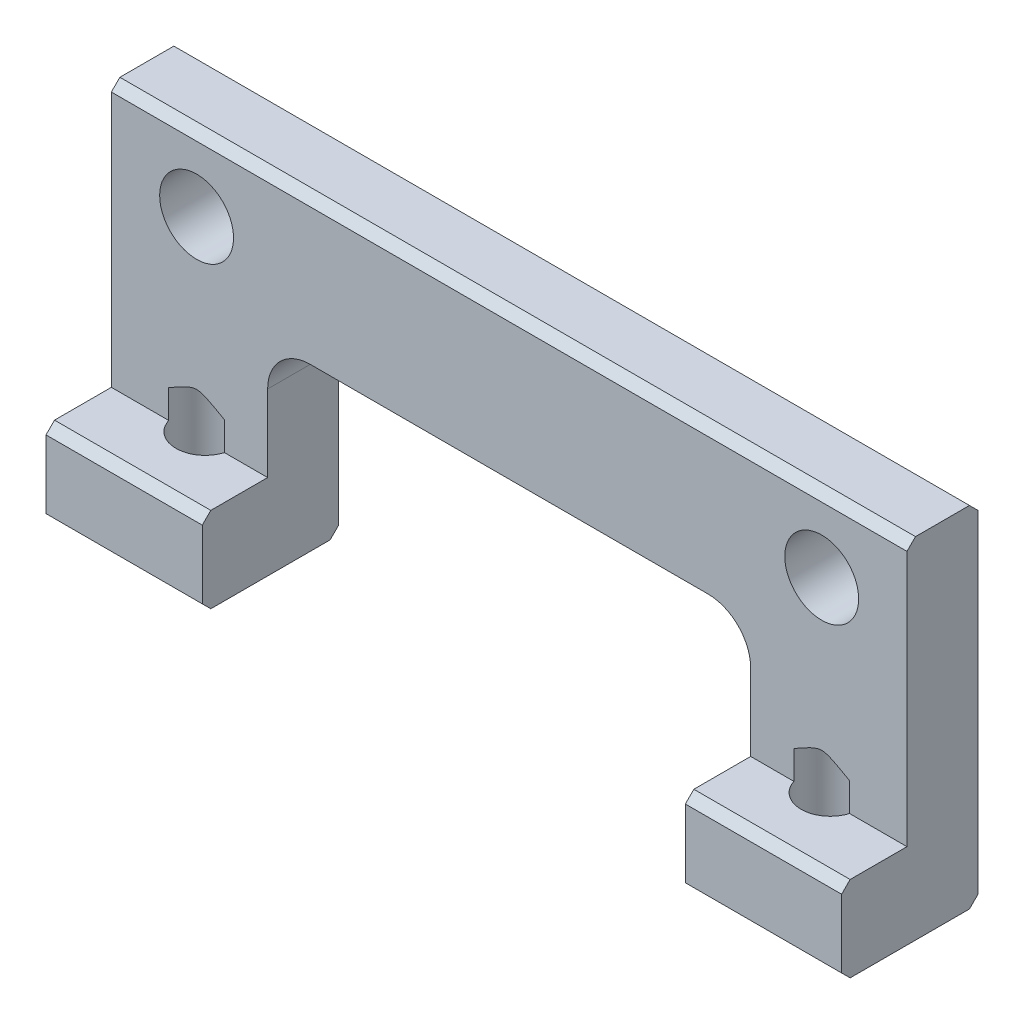
SolidWorks part; units mm, degrees
ref_plane "Front Plane" through (0, 0, 0) normal (0, 0, 1) x (1, 0, 0)
ref_plane "Top Plane" through (0, 0, 0) normal (0, 1, 0) x (1, 0, 0)
ref_plane "Right Plane" through (0, 0, 0) normal (1, 0, 0) x (0, 0, -1)
ref_plane "Plane1" through (0, 0, -2.5) normal (0, 0, -1) x (-1, 0, 0)
sketch "Sketch1" plane through (0, 0, -2.5) normal (0, 0, -1) x (-1, 0, 0)
  line L0 (-8.5, 0) -> (-8.5, 12.3)
  line L1 (-8.5, 12.3) -> (-14, 12.3)
  line L2 (-14, 12.3) -> (-14, 0)
  line L3 (-14, 0) -> (-8.5, 0)
extrude "Boss-Extrude1" add sketch "Sketch1" against normal blind 4.8
sketch "Sketch2" plane through (8.5, 0, 0) normal (-1, 0, 0) x (0, 0, 1)
  line L0 (2.3, 12.3) -> (0, 12.3)
  line L1 (0, 12.3) -> (0, 3)
  line L2 (0, 3) -> (2.3, 3)
  line L3 (2.3, 3) -> (2.3, 12.3)
extrude "Cut-Extrude1" cut sketch "Sketch2" against normal through all
sketch "Sketch3" plane through (8.5, 0, 0) normal (-1, 0, 0) x (0, 0, 1)
  line L0 (0, 7.2) -> (-2.5, 7.2)
  line L1 (-2.5, 7.2) -> (-2.5, 12.3)
  line L2 (-2.5, 12.3) -> (0, 12.3)
  line L3 (0, 12.3) -> (0, 7.2)
extrude "Boss-Extrude2" add sketch "Sketch3" along normal blind 22.5
sketch "Sketch4" plane through (0, 7.2, 0) normal (0, -1, 0) x (1, 0, 0)
  line L0 (-8.5, 0) -> (-8.5, -2.5)
  line L1 (-8.5, -2.5) -> (-14, -2.5)
  line L2 (-14, -2.5) -> (-14, 0)
  line L3 (-14, 0) -> (-8.5, 0)
extrude "Boss-Extrude3" add sketch "Sketch4" along normal blind 7.2
sketch "Sketch5" plane through (0, 0, 0) normal (0, 0, 1) x (1, 0, 0)
  line L0 (-14, 0) -> (-14, 3)
  line L1 (-14, 3) -> (-8.5, 3)
  line L2 (-8.5, 3) -> (-8.5, 0)
  line L3 (-8.5, 0) -> (-14, 0)
extrude "Boss-Extrude4" add sketch "Sketch5" along normal blind 2.3
hole_wizard "Ø2.6 (2.6) Diameter Hole1" positions "Sketch7" profile "Sketch6" hole size "Ø2.6" standard "ANSI Metric"
sketch "Sketch7" plane through (0, 0, -2.5) normal (0, 0, -1) x (-1, 0, 0)
  point P0 (11, 9.7)
  point P1 (-11, 9.7)
sketch "Sketch6" plane through (-11, 9.7, -2.5) normal (1, 0, 0) x (0, 1, 0)
  line L0 (0, 0) -> (0, 4.8)
  line L1 (0, 4.8) -> (1.3, 4.8)
  line L2 (1.3, 4.8) -> (1.3, 0)
  line L5 (1.3, 0) -> (0, 0)
  line L11 (0, -6.35) -> (0, 107.95) construction
  dimension "Thru Hole Dia." = 2.6
  dimension "Thru Hole Depth" = 4.8
hole_wizard "Ø2.05 (2.05) Diameter Hole1" positions "Sketch9" profile "Sketch8" hole size "Ø2.05" standard "ANSI Metric"
sketch "Sketch9" plane through (0, 0, 0) normal (0, -1, 0) x (-1, 0, 0)
  point P0 (-11, 0.3)
  point P1 (11, 0.3)
sketch "Sketch8" plane through (11, 0, -0.3) normal (1, 0, 0) x (0, 0, -1)
  line L0 (0, 0) -> (0, 4.6159)
  line L1 (0, 4.6159) -> (1.025, 4)
  line L2 (1.025, 4) -> (1.025, 0)
  line L5 (1.025, 0) -> (0, 0)
  line L10 (0, 4.6159) -> (-1.025, 4) construction
  line L11 (0, -6.35) -> (0, 107.95) construction
  dimension "Hole Dia." = 2.05
  dimension "Hole Depth" = 4
  dimension "Drill Angle" = 118
chamfer "Chamfer1" distance 0.3 angle 45 11 edges at (11.25, 0, -2.5) (-11.25, 0, -2.5) (11, 0, -1.325) (0, 12.3, 0) (0, 12.3, -2.5) (-11, 0, -1.325) (11, 11, -2.5) (11.25, 0, 2.3) (-11.25, 0, 2.3) (11.25, 3, 2.3) (-11.25, 3, 2.3)
chamfer "Chamfer2" distance 0.2 angle 45 1 edges at (-11, 11, -2.5)
fillet "Fillet1" radius 1.5 2 edges at (-8.5, 7.2, -1.25)
